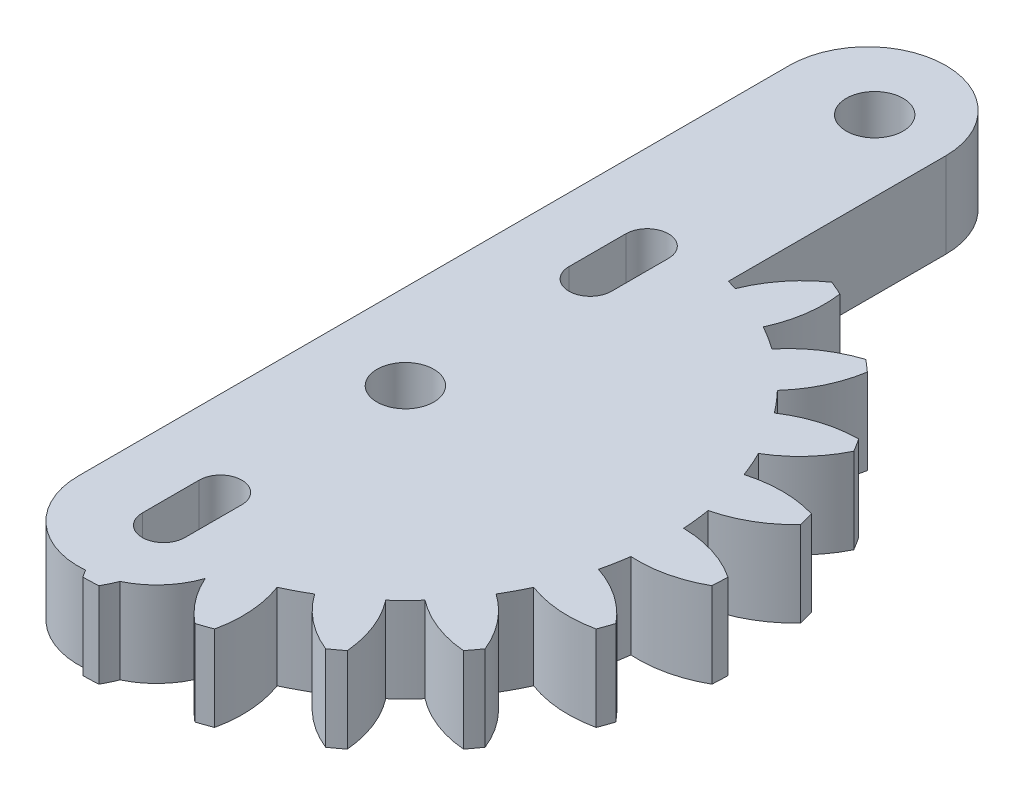
SolidWorks part; units mm, degrees
material "Acrylic (Medium-high impact)"
ref_plane "Front Plane" through (0, 0, 0) normal (0, 0, 1) x (1, 0, 0)
ref_plane "Top Plane" through (0, 0, 0) normal (0, 1, 0) x (1, 0, 0)
ref_plane "Right Plane" through (0, 0, 0) normal (1, 0, 0) x (0, 0, -1)
sketch "Sketch1" plane through (0, 0, 0) normal (0, 1, 0) x (1, 0, 0)
  line L0 (-6, 33) -> (5, 33) construction
  line L1 (5, 33) -> (5, 0)
  line L2 (-6, 0) -> (-6, 33)
  line L3 (-6, 0) -> (-6, -17)
  line L5 (5, -17) -> (5, 0)
  arc A0 (5, -17) -> (-6, -17) centre (-0.5, -17) cw
  arc A1 (5, 33) -> (-6, 33) centre (-0.5, 33) ccw
  dimension "D1" = 33
  dimension "D2" = 17
extrude "Boss-Extrude1" add sketch "Sketch1" along normal blind 6
sketch "Sketch4" plane through (0, 6, 0) normal (0, 1, 0) x (1, 0, 0)
  line L0 (0, 18.4053) -> (0, -22.4867)
  arc A1 (15.4112, 17.0732) -> (14.5856, 17.7837) centre (0, 0) ccw
  arc A2 (13.365, 12.7902) -> (15.4112, 17.0732) centre (7.1175, 18.4053) ccw
  arc A3 (14.6393, 11.3095) -> (13.365, 12.7902) centre (0, 0) ccw
  arc A4 (19.1794, 12.6945) -> (14.6393, 11.3095) centre (19.2605, 4.2949) ccw
  arc A5 (19.759, 11.7721) -> (19.1794, 12.6945) centre (0, 0) ccw
  arc A6 (16.5412, 8.2826) -> (19.759, 11.7721) centre (12.2264, 15.4896) ccw
  arc A7 (17.3224, 6.492) -> (16.5412, 8.2826) centre (0, 0) ccw
  arc A8 (22.0691, 6.4773) -> (17.3224, 6.492) centre (19.6707, -1.5731) ccw
  arc A9 (22.351, 5.4251) -> (22.0691, 6.4773) centre (0, 0) ccw
  arc A10 (18.2477, 3.039) -> (22.351, 5.4251) centre (16.2488, 11.1977) ccw
  arc A11 (18.4664, 1.0977) -> (18.2477, 3.039) centre (0, 0) ccw
  arc A12 (22.9978, -0.3155) -> (18.4664, 1.0977) centre (18.3332, -7.3012) ccw
  arc A13 (22.9571, -1.404) -> (22.9978, -0.3155) centre (0, 0) ccw
  arc A14 (18.3327, -2.4746) -> (22.9571, -1.404) centre (18.8275, 5.9108) ccw
  arc A15 (17.9695, -4.3941) -> (18.3327, -2.4746) centre (0, 0) ccw
  arc A16 (21.8831, -7.0802) -> (17.9695, -4.3941) centre (15.3666, -12.3807) ccw
  arc A17 (21.5233, -8.1084) -> (21.8831, -7.0802) centre (0, 0) ccw
  arc A18 (16.7889, -7.7684) -> (21.5233, -8.1084) centre (19.7333, 0.0987) ccw
  arc A19 (15.876, -9.4955) -> (16.7889, -7.7684) centre (0, 0) ccw
  arc A20 (18.824, -13.2158) -> (15.876, -9.4955) centre (11.0346, -16.36) ccw
  arc A21 (18.1771, -14.0923) -> (18.824, -13.2158) centre (0, 0) ccw
  arc A22 (13.7532, -12.3718) -> (18.1771, -14.0923) centre (18.8857, -5.7222) ccw
  arc A23 (12.3718, -13.7532) -> (13.7532, -12.3718) centre (0, 0) ccw
  arc A24 (14.0923, -18.1771) -> (12.3718, -13.7532) centre (5.7222, -18.8857) ccw
  arc A25 (13.2158, -18.824) -> (14.0923, -18.1771) centre (0, 0) ccw
  arc A26 (9.4955, -15.876) -> (13.2158, -18.824) centre (16.36, -11.0346) ccw
  arc A27 (7.7684, -16.7889) -> (9.4955, -15.876) centre (0, 0) ccw
  arc A28 (8.1084, -21.5233) -> (7.7684, -16.7889) centre (-0.0987, -19.7333) ccw
  arc A29 (7.0802, -21.8831) -> (8.1084, -21.5233) centre (0, 0) ccw
  arc A30 (4.3941, -17.9695) -> (7.0802, -21.8831) centre (12.3807, -15.3666) ccw
  arc A31 (2.4746, -18.3327) -> (4.3941, -17.9695) centre (0, 0) ccw
  arc A32 (1.404, -22.9571) -> (2.4746, -18.3327) centre (-5.9108, -18.8275) ccw
  arc A33 (0.3155, -22.9978) -> (1.404, -22.9571) centre (0, 0) ccw
  arc A34 (0, -22.4867) -> (0.3155, -22.9978) centre (7.3012, -18.3332) ccw
  arc A79 (5.6895, 17.5038) -> (0, 18.4053) centre (0, 0) ccw
  arc A80 (8.6957, 21.2928) -> (5.6895, 17.5038) centre (13.4944, 14.3984) ccw
  arc A81 (9.6941, 20.8572) -> (8.6957, 21.2928) centre (0, 0) ccw
  arc A82 (9.0013, 16.1614) -> (9.6941, 20.8572) centre (1.3763, 19.6855) ccw
  arc A83 (10.6554, 15.122) -> (9.0013, 16.1614) centre (0, 0) ccw
  arc A84 (14.5856, 17.7837) -> (10.6554, 15.122) centre (17.1389, 9.7812) ccw
extrude "Boss-Extrude2" add sketch "Sketch4" against normal blind 6
sketch "Sketch2" plane through (0, 6, 0) normal (0, 1, 0) x (1, 0, 0)
  line L0 (-7.3626, 16.5) -> (11.1888, 16.5) construction
  line L1 (1.5, 17) -> (1.5, 13)
  line L2 (-1.5, 17) -> (-1.5, 13)
  line L3 (-1000, 0) -> (49000, 0) construction
  line L4 (-1.5, -17) -> (-1.5, -13)
  line L5 (1.5, -17) -> (1.5, -13)
  circle A0 centre (0, 0) radius 2
  circle A1 centre (0, 33) radius 2
  arc A2 (-1.5, 17) -> (1.5, 17) centre (0, 17) cw
  arc A3 (1.5, 13) -> (-1.5, 13) centre (0, 13) cw
  arc A4 (1.5, -13) -> (-1.5, -13) centre (0, -13) ccw
  arc A5 (-1.5, -17) -> (1.5, -17) centre (0, -17) ccw
  dimension "D1" = 33
extrude "Cut-Extrude1" cut sketch "Sketch2" against normal through all
